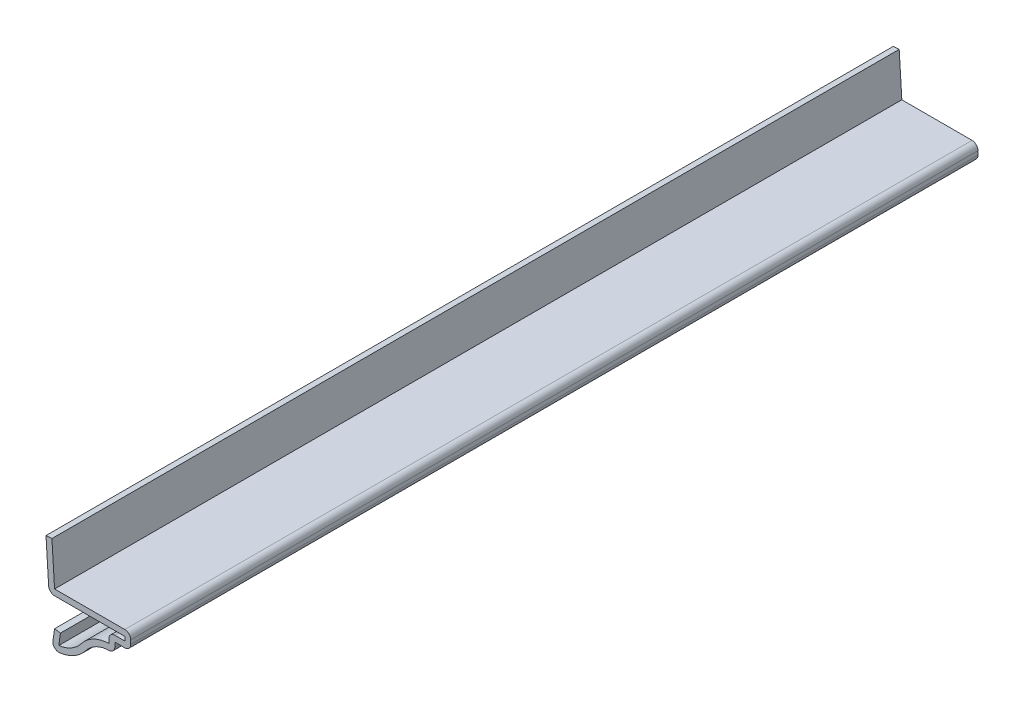
SolidWorks part; units mm, degrees
ref_plane "Front Plane" through (0, 0, 0) normal (0, 0, 1) x (1, 0, 0)
ref_plane "Top Plane" through (0, 0, 0) normal (0, 1, 0) x (1, 0, 0)
ref_plane "Right Plane" through (0, 0, 0) normal (1, 0, 0) x (0, 0, -1)
sketch "Sketch1" plane through (0, 0, 0) normal (0, 0, 1) x (1, 0, 0)
  line L0 (0, 0) -> (0, 18.5386) construction
  line L1 (0, 14.2875) -> (0.3969, 7.9375)
  line L2 (0.3969, 7.9375) -> (11.811, 7.9375)
  line L3 (11.811, 7.9375) -> (11.811, 5.5563)
  line L4 (11.811, 5.5563) -> (9.4297, 5.5563)
  line L5 (9.4297, 5.5563) -> (9.4297, 3.9688)
  line L6 (0, 0) -> (0.3969, 2.7781)
  arc A0 (9.4297, 3.9688) -> (5.1129, 2.3069) centre (8.636, -0.407) ccw
  arc A1 (5.1129, 2.3069) -> (0, 0) centre (0.3969, 5.9399) cw
  point P12 (9.4297, 4.7625)
  point P13 (0, 0)
  point P15 (5.3494, 2.3357)
  dimension "D3" = 0.3969
  dimension "D12" = 5.9531
  dimension "D1" = 11.811
  dimension "D2" = 6.35
  dimension "D4" = 0.7937
  dimension "D5" = 2.3813
  dimension "D6" = 7.9375
  dimension "D7" = 2.3813
  dimension "D8" = 9.4298
  dimension "D9" = 2.7781
  dimension "D10" = 0.3969
  dimension "D11" = 1.5875
extrude "Extrude-Thin1" add sketch "Sketch1" against normal blind 127 thin
fillet "Fillet1" radius 0.889 6 edges at (11.811, 5.5563, -63.5) (11.811, 7.9375, -63.5) (8.5407, 6.4453, -63.5) (9.4297, 3.9688, -63.5) (0, 0, -63.5) (-0.4383, 7.0485, -63.5)
